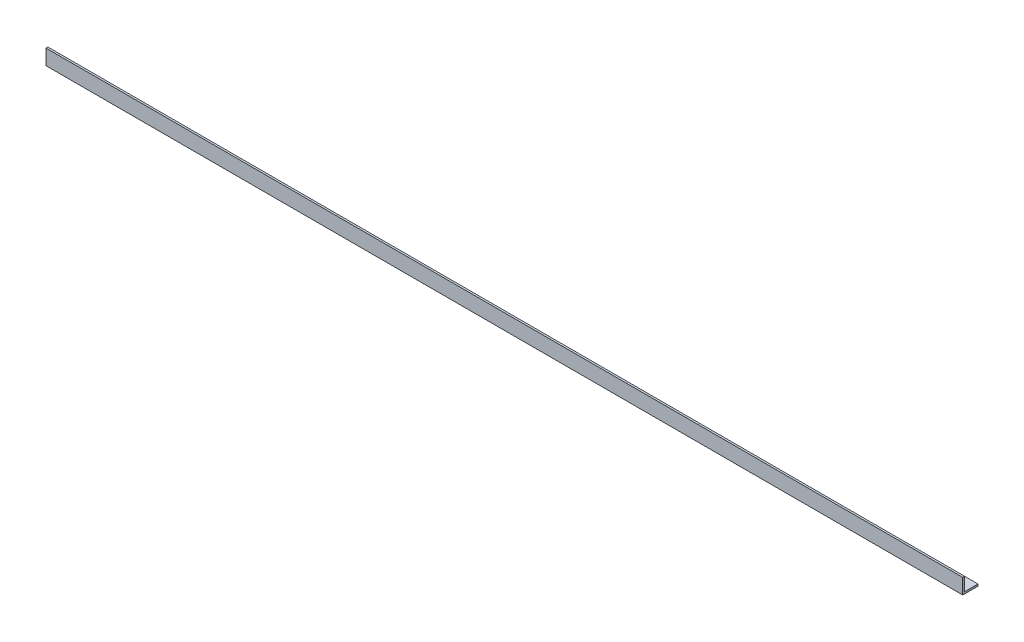
SolidWorks part; units mm, degrees
ref_plane "Front Plane" through (0, 0, 0) normal (0, 0, 1) x (1, 0, 0)
ref_plane "Top Plane" through (0, 0, 0) normal (0, 1, 0) x (1, 0, 0)
ref_plane "Right Plane" through (0, 0, 0) normal (1, 0, 0) x (0, 0, -1)
sketch "Sketch2" plane through (0, 0, 0) normal (1, 0, 0) x (0, 0, -1)
  line L0 (0, 0) -> (0, 25.4)
  line L1 (0, 25.4) -> (3.175, 25.4)
  line L2 (3.175, 25.4) -> (3.175, 3.175)
  line L3 (3.175, 3.175) -> (25.4, 3.175)
  line L4 (25.4, 3.175) -> (25.4, 0)
  line L5 (25.4, 0) -> (0, 0)
  dimension "D1" = 25.4
  dimension "D2" = 3.175
extrude "Boss-Extrude2" add sketch "Sketch2" along normal mid plane 1524
